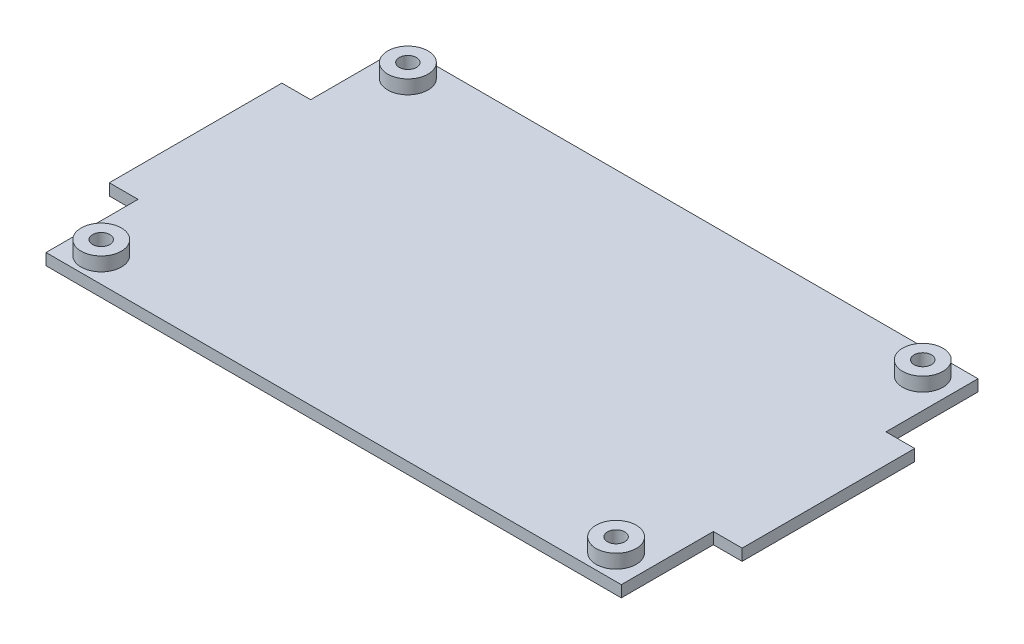
SolidWorks part; units mm, degrees
ref_plane "前视基准面" through (0, 0, 0) normal (0, 0, 1) x (1, 0, 0)
ref_plane "上视基准面" through (0, 0, 0) normal (0, 1, 0) x (1, 0, 0)
ref_plane "右视基准面" through (0, 0, 0) normal (1, 0, 0) x (0, 0, -1)
sketch "草图1" plane through (0, 0, 0) normal (0, 1, 0) x (1, 0, 0)
  line L1 (-50, 31) -> (50, 31)
  line L2 (-50, 31) -> (-50, -31)
  line L3 (-50, -31) -> (50, -31)
  line L4 (50, 31) -> (50, -31)
  line L5 (-50, 31) -> (50, -31) construction
  line L6 (-50, -31) -> (50, 31) construction
  line L7 (-55, 15) -> (55, 15)
  line L8 (-55, 15) -> (-55, -15)
  line L9 (-55, -15) -> (55, -15)
  line L10 (55, 15) -> (55, -15)
  line L11 (-55, 15) -> (55, -15) construction
  line L12 (-55, -15) -> (55, 15) construction
  point P0 (0, 0)
  point P6 (0, 0)
  dimension "D1" = 62
  dimension "D2" = 100
  dimension "D3" = 110
  dimension "D4" = 30
extrude "底板" add sketch "草图1" along normal blind 2 contours L8 L9 L10 L7 | L1 L4 L3 L2
sketch "草图2" plane through (0, 2, 0) normal (0, 1, 0) x (1, 0, 0)
  line L1 (-44.75, 26.65) -> (44.75, 26.65)
  line L2 (-44.75, 26.65) -> (-44.75, -26.65)
  line L3 (-44.75, -26.65) -> (44.75, -26.65)
  line L4 (44.75, 26.65) -> (44.75, -26.65)
  line L5 (-44.75, 26.65) -> (44.75, -26.65) construction
  line L6 (-44.75, -26.65) -> (44.75, 26.65) construction
  circle A0 centre (-44.75, 26.65) radius 1.5
  circle A1 centre (44.75, 26.65) radius 1.5
  circle A2 centre (-44.75, -26.65) radius 1.5
  circle A3 centre (44.75, -26.65) radius 1.5
  point P0 (0, 0)
  dimension "D3" = 3
  dimension "D4" = 3
  dimension "D5" = 3
  dimension "D6" = 3
  dimension "D1" = 53.3
  dimension "D2" = 89.5
extrude "螺丝孔" cut sketch "草图2" against normal blind 2 contours A0 | A2 | A3 | A1
sketch "草图3" plane through (0, 2, 0) normal (0, 1, 0) x (1, 0, 0)
  circle A0 centre (-44.75, 26.65) radius 1.5 construction
  circle A1 centre (-44.75, 26.65) radius 1.5
  circle A2 centre (44.75, 26.65) radius 1.5 construction
  circle A3 centre (44.75, 26.65) radius 1.5
  circle A4 centre (-44.75, -26.65) radius 1.5 construction
  circle A5 centre (-44.75, -26.65) radius 1.5
  circle A6 centre (44.75, -26.65) radius 1.5 construction
  circle A7 centre (44.75, -26.65) radius 1.5
  circle A8 centre (-44.75, 26.65) radius 3.5
  circle A9 centre (44.75, 26.65) radius 3.5
  circle A10 centre (-44.75, -26.65) radius 3.5
  circle A11 centre (44.75, -26.65) radius 3.5
  dimension "D1" = 2
extrude "螺丝凸起" add sketch "草图3" along normal blind 2.4
